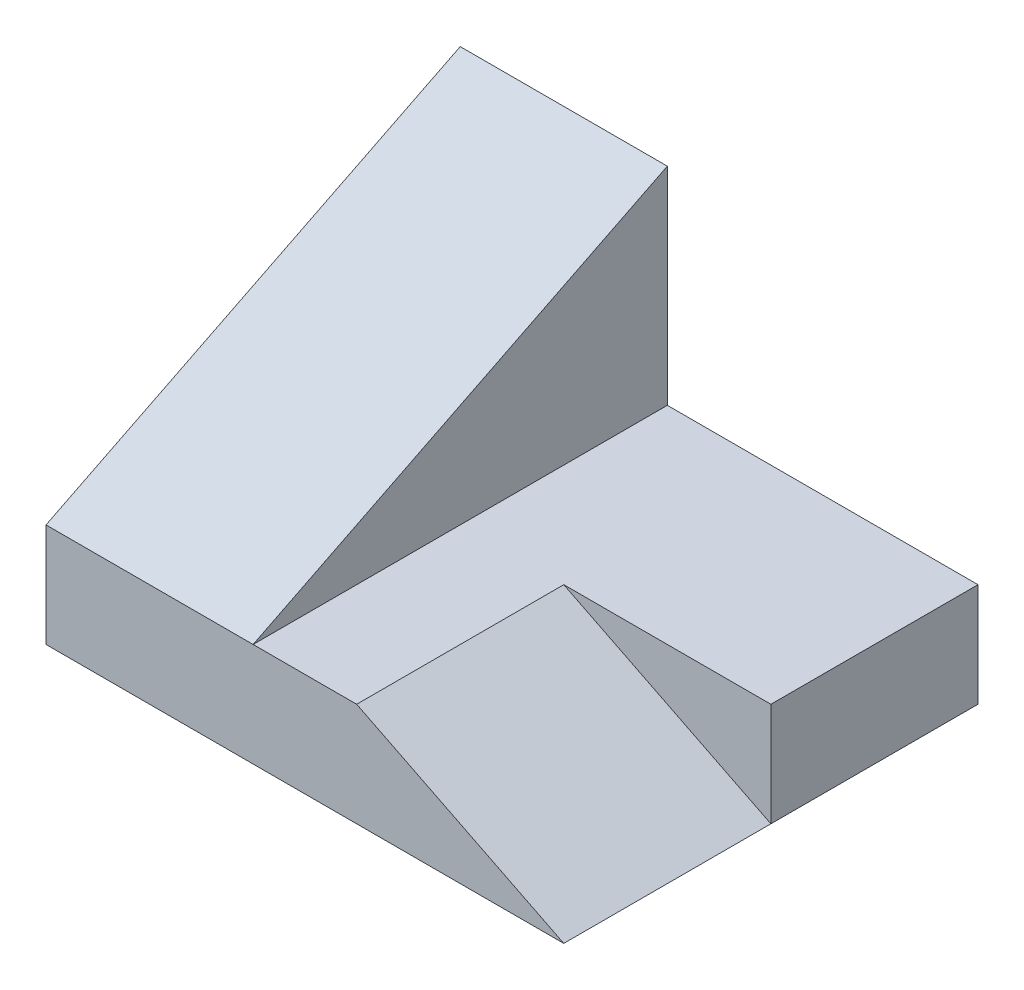
SolidWorks part; units mm, degrees
ref_plane "Front Plane" through (0, 0, 0) normal (0, 0, 1) x (1, 0, 0)
ref_plane "Top Plane" through (0, 0, 0) normal (0, 1, 0) x (1, 0, 0)
ref_plane "Right Plane" through (0, 0, 0) normal (1, 0, 0) x (0, 0, -1)
sketch "Sketch1" plane through (0, 0, 0) normal (0, 1, 0) x (1, 0, 0)
  line L0 (0, 0) -> (50, 0)
  line L1 (50, 0) -> (50, 40)
  line L2 (50, 40) -> (0, 40)
  line L3 (0, 40) -> (0, 0)
  dimension "D1" = 50
  dimension "D2" = 40
extrude "Boss-Extrude1" add sketch "Sketch1" along normal blind 30
sketch "Sketch2" plane through (0, 30, 0) normal (0, 1, 0) x (1, 0, 0)
  line L0 (0, 20) -> (50, 20) construction
  line L1 (0, 40) -> (0, 0) construction
  line L2 (50, 0) -> (50, 40) construction
  line L3 (25, 40) -> (25, 0) construction
  line L4 (0, 0) -> (50, 0) construction
  line L6 (50, 40) -> (20, 40)
  line L7 (50, 40) -> (50, 0)
  line L8 (50, 0) -> (20, 0)
  line L9 (20, 40) -> (20, 0)
  point P11 (25, 20)
  dimension "D1" = 30
extrude "Cut-Extrude1" cut sketch "Sketch2" against normal blind 20
sketch "Sketch4" plane through (20, 0, 0) normal (1, 0, 0) x (0, 0, -1)
  line L0 (40, 30) -> (0, 10)
  line L1 (0, 10) -> (0, 30)
  line L2 (0, 30) -> (40, 30)
extrude "Cut-Extrude2" cut sketch "Sketch4" against normal blind 20
sketch "Sketch5" plane through (0, 0, 0) normal (0, 0, 1) x (1, 0, 0)
  line L0 (50, 0) -> (30, 10)
  line L1 (20, 10) -> (50, 10) construction
  line L2 (30, 10) -> (50, 10)
  line L3 (50, 10) -> (50, 0)
  dimension "D1" = 20
extrude "Cut-Extrude3" cut sketch "Sketch5" against normal blind 20
